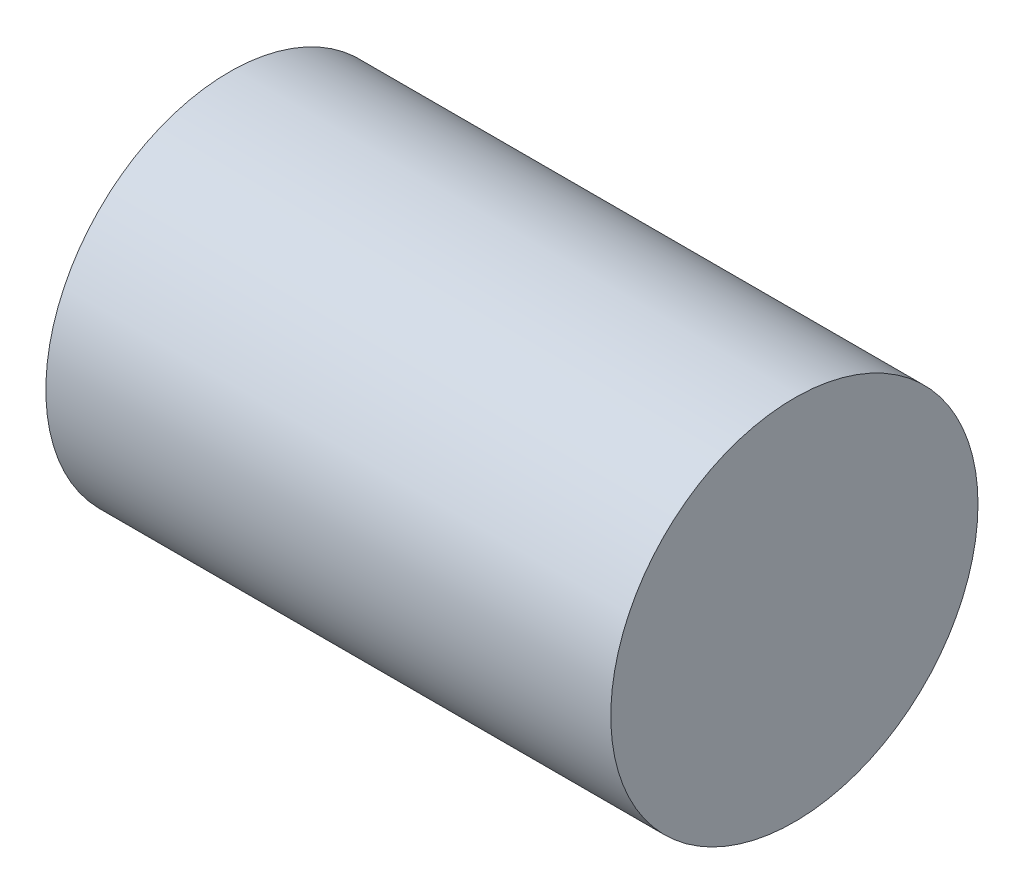
SolidWorks part; units mm, degrees
ref_plane "Front Plane" through (0, 0, 0) normal (0, 0, 1) x (1, 0, 0)
ref_plane "Top Plane" through (0, 0, 0) normal (0, 1, 0) x (1, 0, 0)
ref_plane "Right Plane" through (0, 0, 0) normal (1, 0, 0) x (0, 0, -1)
sketch "Sketch1" plane through (0, 0, 0) normal (1, 0, 0) x (0, 0, -1)
  circle A0 centre (0, 0) radius 19.5
  dimension "D1" = 39
extrude "Boss-Extrude1" add sketch "Sketch1" along normal blind 60
